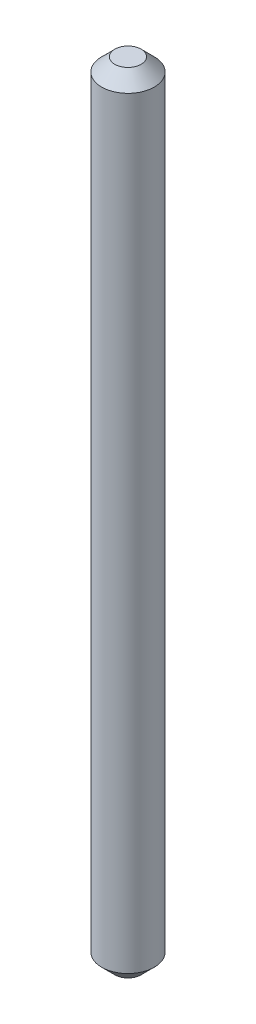
SolidWorks part; units mm, degrees
ref_plane "Płaszczyzna przednia" through (0, 0, 0) normal (0, 0, 1) x (1, 0, 0)
ref_plane "Płaszczyzna górna" through (0, 0, 0) normal (0, 1, 0) x (1, 0, 0)
ref_plane "Płaszczyzna prawa" through (0, 0, 0) normal (1, 0, 0) x (0, 0, -1)
sketch "Szkic1" plane through (0, 0, 0) normal (0, 1, 0) x (1, 0, 0)
  circle A0 centre (0, 0) radius 1
  dimension "D1" = 2
extrude "Dodanie-wyciągnięcie1" add sketch "Szkic1" along normal mid plane 30
chamfer "Sfazowanie1" distance 0.5 angle 45 2 edges at (0, -15, 1) (0, 15, 1)
